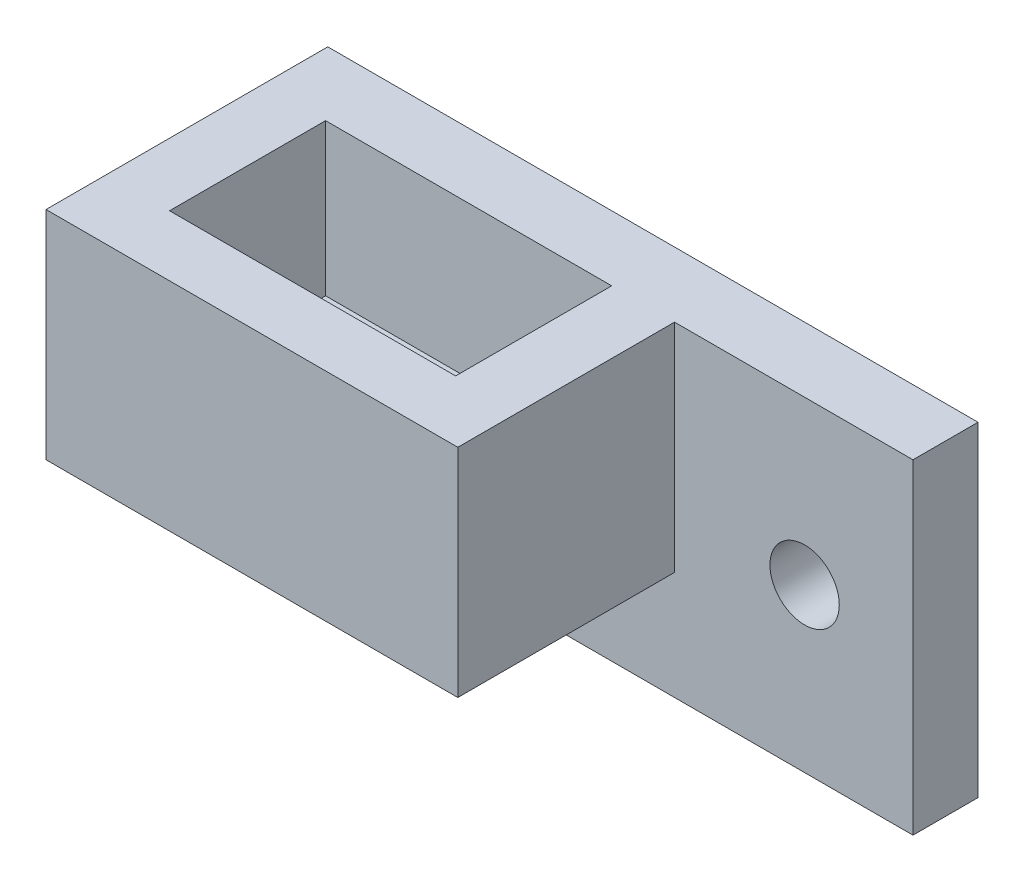
SolidWorks part; units mm, degrees
ref_plane "Alzado" through (0, 0, 0) normal (0, 0, 1) x (1, 0, 0)
ref_plane "Planta" through (0, 0, 0) normal (0, 1, 0) x (1, 0, 0)
ref_plane "Vista lateral" through (0, 0, 0) normal (1, 0, 0) x (0, 0, -1)
sketch "Croquis1" plane through (0, 0, 0) normal (0, 0, 1) x (1, 0, 0)
  line L0 (-13.2998, 0) -> (-28.2998, 0)
  line L1 (-43.2998, 15) -> (-13.2998, 15)
  line L4 (-13.2998, 15) -> (-13.2998, 0)
  line L5 (-13.2998, 7.5) -> (-18.2998, 7.5) construction
  line L6 (-28.2998, 0) -> (-28.2998, 5)
  line L7 (-28.2998, 5) -> (-43.2998, 5)
  line L8 (-43.2998, 5) -> (-43.2998, 15)
  circle A0 centre (-18.2998, 7.5) radius 1.6
  dimension "D3" = 5
  dimension "D1" = 15
  dimension "D2" = 30
  dimension "D4" = 5
extrude "Saliente-Extruir1" add sketch "Croquis1" along normal blind 3
sketch "Croquis2" plane through (0, 0, 3) normal (0, 0, 1) x (1, 0, 0)
  line L1 (-43.2998, 15) -> (-24.2998, 15)
  line L2 (-43.2998, 15) -> (-43.2998, 5)
  line L3 (-43.2998, 5) -> (-24.2998, 5)
  line L4 (-24.2998, 15) -> (-24.2998, 5)
  dimension "D1" = 19
extrude "Saliente-Extruir2" add sketch "Croquis2" along normal blind 10
sketch "Croquis3" plane through (0, 15, 0) normal (0, 1, 0) x (1, 0, 0)
  line L0 (-24.2998, -13) -> (-43.2998, -13) construction
  line L1 (-27.1998, -10.2) -> (-40.3998, -10.2)
  line L2 (-27.1998, -10.2) -> (-27.1998, -3)
  line L3 (-27.1998, -3) -> (-40.3998, -3)
  line L4 (-40.3998, -10.2) -> (-40.3998, -3)
  line L5 (-24.2998, -13) -> (-24.2998, -3) construction
  line L6 (-43.2998, -13) -> (-43.2998, 0) construction
  dimension "D1" = 7.2
  dimension "D2" = 2.8
  dimension "D3" = 2.9
  dimension "D4" = 2.9
extrude "Cortar-Extruir1" cut sketch "Croquis3" against normal blind 7
sketch "Croquis4" plane through (0, 8, 0) normal (0, 1, 0) x (1, 0, 0)
  circle A0 centre (-33.7998, -6.5) radius 3.2
extrude "Cortar-Extruir2" cut sketch "Croquis4" against normal up to vertex (3 mm away)
sketch "Croquis5" plane through (-28.2998, 0, 0) normal (-1, 0, 0) x (0, 0, 1)
  line L1 (3, 5) -> (-7, 5)
  line L2 (3, 5) -> (3, 0)
  line L3 (3, 0) -> (-7, 0)
  line L4 (-7, 5) -> (-7, 0)
  dimension "D1" = 10
extrude "Saliente-Extruir3" add sketch "Croquis5" along normal blind 3
